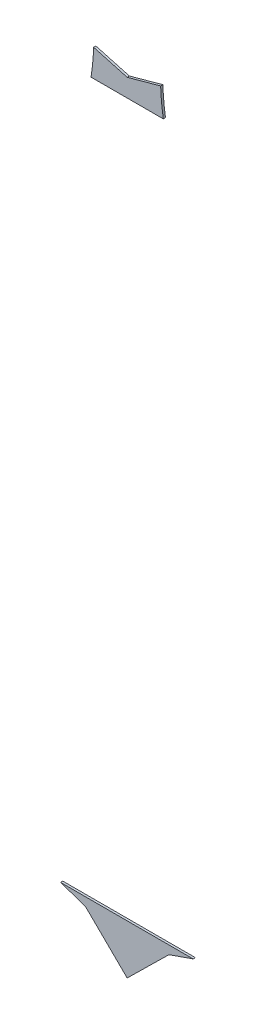
SolidWorks part; units mm, degrees
ref_plane "Alzado" through (0, 0, 0) normal (0, 0, 1) x (1, 0, 0)
ref_plane "Planta" through (0, 0, 0) normal (0, 1, 0) x (1, 0, 0)
ref_plane "Vista lateral" through (0, 0, 0) normal (1, 0, 0) x (0, 0, -1)
sketch "Model" plane through (0, 0, 0) normal (0, 0, 1) x (1, 0, 0)
  line L0 (39.2658, -0.9116) -> (33.3111, -0.9116)
  line L1 (34.6779, 31.0884) -> (37.9228, 31.0884)
  line L2 (37.8039, 32.3102) -> (36.3018, 31.8953)
  line L3 (34.7966, 32.3101) -> (36.3018, 31.8953)
  line L4 (39.2658, -0.9116) -> (38.1773, -1.291)
  line L5 (38.1773, -1.291) -> (36.3019, -3.135)
  line L6 (36.3019, -3.135) -> (34.4264, -1.2912)
  line L7 (34.4264, -1.2912) -> (33.3111, -0.9116)
  arc A0 (34.6779, 31.0884) -> (34.7966, 32.3101) centre (24.7935, 32.6659) ccw
  arc A1 (37.8039, 32.3102) -> (37.9228, 31.0884) centre (47.807, 32.667) ccw
extrude "Saliente-Extruir1" add sketch "Model" along normal blind 0.1
